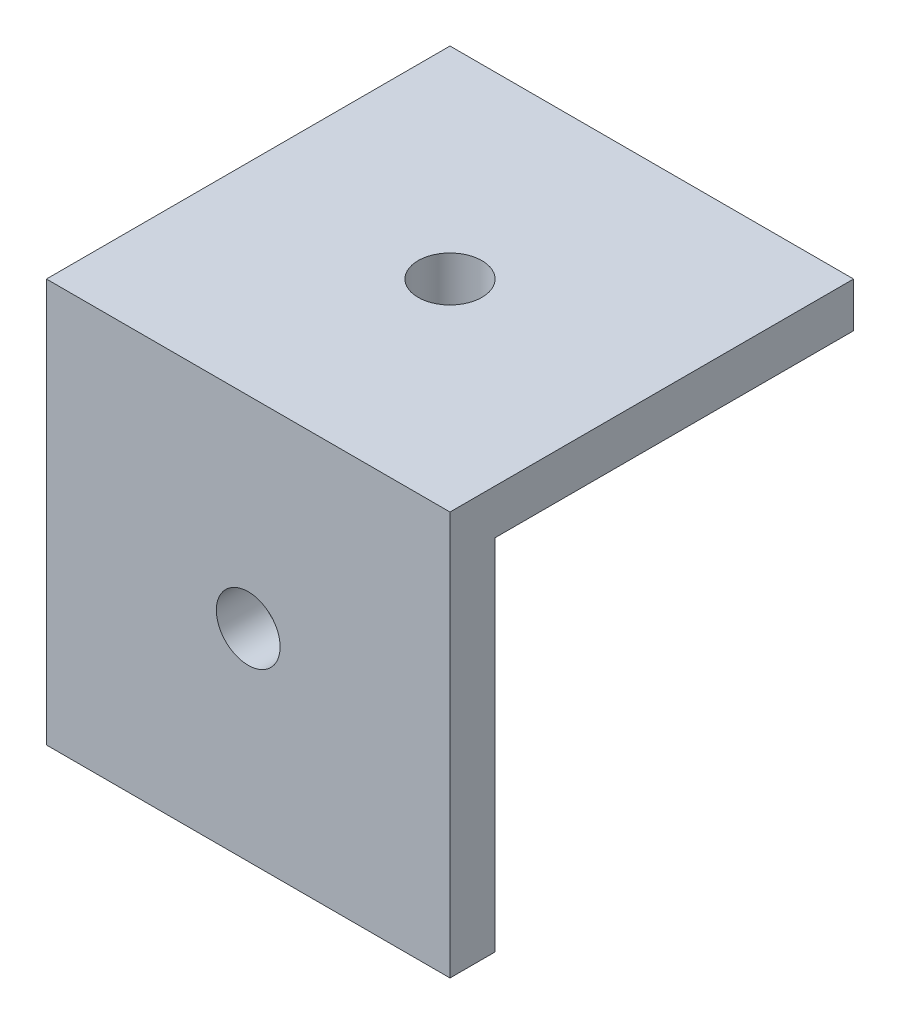
SolidWorks part; units mm, degrees
ref_plane "Front Plane" through (0, 0, 0) normal (0, 0, 1) x (1, 0, 0)
ref_plane "Top Plane" through (0, 0, 0) normal (0, 1, 0) x (1, 0, 0)
ref_plane "Right Plane" through (0, 0, 0) normal (1, 0, 0) x (0, 0, -1)
sketch "Sketch2" plane through (0, 0, 0) normal (0, 1, 0) x (1, 0, 0)
  line L1 (-9, -9) -> (9, -9)
  line L2 (-9, -9) -> (-9, 9)
  line L3 (-9, 9) -> (9, 9)
  line L4 (9, -9) -> (9, 9)
  line L5 (-9, -9) -> (9, 9) construction
  line L6 (-9, 9) -> (9, -9) construction
  point P0 (0, 0)
  dimension "D1" = 18
  dimension "D2" = 18
extrude "Boss-Extrude1" add sketch "Sketch2" along normal blind 18
sketch "Sketch3" plane through (0, 18, 0) normal (0, 1, 0) x (1, 0, 0)
  circle A0 centre (0, 0) radius 1.4224
  dimension "D1" = 2.8448
extrude "Cut-Extrude1" cut sketch "Sketch3" against normal blind 6.6
sketch "Sketch4" plane through (9, 0, 0) normal (1, 0, 0) x (0, 0, -1)
  line L0 (-9, 18) -> (-9, 0) construction
  line L1 (-9, 0) -> (9, 0) construction
  circle A0 centre (0, 9) radius 1.4224
  dimension "D3" = 2.8448
  dimension "D1" = 9
  dimension "D2" = 9
extrude "Cut-Extrude2" cut sketch "Sketch4" against normal blind 6.6
sketch "Sketch5" plane through (0, 0, 9) normal (0, 0, 1) x (1, 0, 0)
  line L0 (-9, 0) -> (9, 0) construction
  line L1 (9, 18) -> (9, 0) construction
  circle A0 centre (0, 9) radius 1.4224
  dimension "D1" = 2.8448
  dimension "D2" = 9
  dimension "D3" = 9
extrude "Cut-Extrude3" cut sketch "Sketch5" against normal blind 6.6
sketch "Sketch6" plane through (0, 0, -9) normal (0, 0, -1) x (-1, 0, 0)
  line L0 (9, 18) -> (9, 0) construction
  line L1 (9, 16) -> (-7, 16)
  line L2 (9, 16) -> (9, 0)
  line L3 (9, 0) -> (-7, 0)
  line L4 (-7, 16) -> (-7, 0)
  line L5 (-9, 0) -> (9, 0) construction
  line L6 (-9, 18) -> (9, 18) construction
  line L7 (-9, 18) -> (-9, 0) construction
  dimension "D1" = 2
  dimension "D2" = 2
extrude "Cut-Extrude4" cut sketch "Sketch6" against normal blind 16
sketch "Sketch7" plane through (7, 0, 0) normal (-1, 0, 0) x (0, 0, 1)
  line L0 (7, 16) -> (-9, 16) construction
  line L1 (-9, 0) -> (7, 0)
  line L2 (-9, 0) -> (-9, 16)
  line L3 (-9, 16) -> (7, 16)
  line L4 (7, 0) -> (7, 16)
extrude "Cut-Extrude5" cut sketch "Sketch7" against normal blind 10
